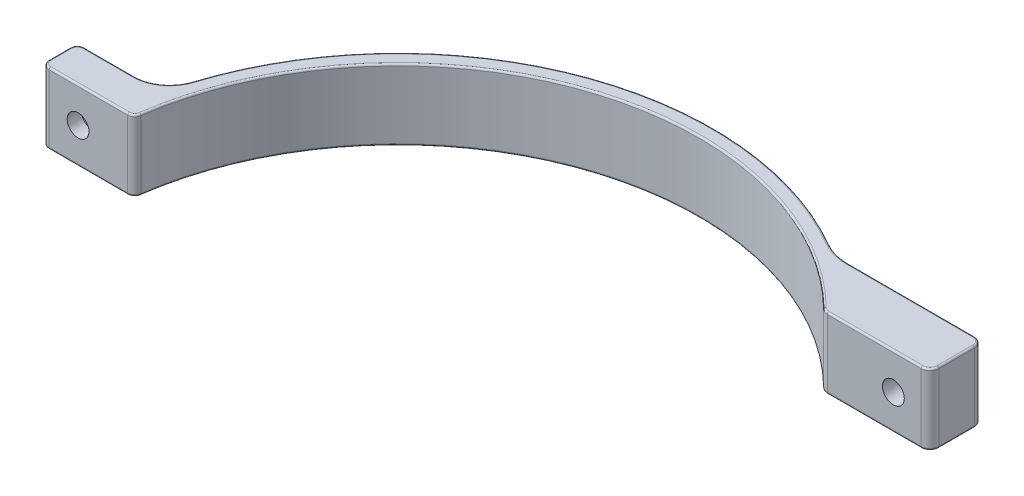
SolidWorks part; units mm, degrees
material "PVC 0.007 Plasticizado"
ref_plane "Plano frontal" through (0, 0, 0) normal (0, 0, 1) x (1, 0, 0)
ref_plane "Plano superior" through (0, 0, 0) normal (0, 1, 0) x (1, 0, 0)
ref_plane "Plano direito" through (0, 0, 0) normal (1, 0, 0) x (0, 0, -1)
sketch "Esboço1" plane through (0, 0, 0) normal (0, 1, 0) x (1, 0, 0)
  line L0 (0, -1000) -> (0, 49000) construction
  line L1 (-1000, 0) -> (49000, 0) construction
  line L3 (61.2372, 60) -> (87.708, 60)
  line L4 (90.208, 62.5) -> (90.208, 72.5)
  line L5 (87.708, 75) -> (52.1153, 75)
  line L7 (-108.4097, 20) -> (-94.3451, 20)
  line L8 (-110.4097, 18) -> (-110.4097, 12)
  line L9 (-108.4097, 10) -> (-86.1684, 10)
  arc A0 (59.4876, 60.7143) -> (-84.1876, 11.7241) centre (0, 0) ccw
  arc A1 (44.5986, 77.0192) -> (-84.8153, 26.9697) centre (0, 0) ccw
  circle A2 centre (0, 0) radius 85 construction
  circle A3 centre (0, 0) radius 89 construction
  arc A4 (44.5986, 77.0192) -> (52.1153, 75) centre (52.1153, 90) ccw
  arc A5 (90.208, 72.5) -> (87.708, 75) centre (87.708, 72.5) ccw
  arc A6 (87.708, 60) -> (90.208, 62.5) centre (87.708, 62.5) ccw
  arc A7 (59.4876, 60.7143) -> (61.2372, 60) centre (61.2372, 62.5) ccw
  arc A11 (-94.3451, 20) -> (-84.8153, 26.9697) centre (-94.3451, 30) ccw
  arc A12 (-84.1876, 11.7241) -> (-86.1684, 10) centre (-86.1684, 12) cw
  arc A13 (-108.4097, 10) -> (-110.4097, 12) centre (-108.4097, 12) cw
  arc A14 (-108.4097, 20) -> (-110.4097, 18) centre (-108.4097, 18) ccw
  point P9 (-177.2056, 15)
  point P25 (90.208, 75)
  point P28 (90.208, 60)
  point P31 (60.208, 60)
  point P34 (-84.4097, 10)
  point P37 (-110.4097, 10)
  point P49 (-110.4097, 10)
  dimension "D1" = 4
  dimension "D4" = 170
  dimension "D5" = 60
  dimension "D8" = 15
  dimension "D9" = 2.5
  dimension "D10" = 2
  dimension "D11" = 10
  dimension "D13" = 2
  dimension "D14" = 2
  dimension "D2" = 26
  dimension "D3" = 15
  dimension "D6" = 30
  dimension "D7" = 10
  dimension "D12" = 10
extrude "Ressalto-extrusão1" add sketch "Esboço1" along normal blind 20
sketch "Esboço3" plane through (0, 0, -60) normal (0, 0, 1) x (1, 0, 0)
  line L1 (61.2372, 20) -> (59.4876, 20) construction
  circle A0 centre (79.8624, 9.7994) radius 3.075
  point P4 (60.3624, 20)
  dimension "D1" = 19.5
extrude "Corte-extrusão1" cut sketch "Esboço3" against normal blind 20
sketch "Esboço4" plane through (0, 0, -75) normal (0, 0, -1) x (-1, 0, 0)
  circle A0 centre (-79.8624, 9.7994) radius 5.25
extrude "Corte-extrusão2" cut sketch "Esboço4" against normal blind 6
sketch "Esboço5" plane through (0, 0, -10) normal (0, 0, 1) x (1, 0, 0)
  line L0 (-108.4097, 20) -> (-86.1684, 20) construction
  line L5 (-108.4097, 20) -> (-108.4097, 0) construction
  circle A0 centre (-100.1797, 10) radius 3.075
  dimension "D1" = 6.15
  dimension "D2" = 10
  dimension "D3" = 8.23
extrude "Corte-extrusão3" cut sketch "Esboço5" against normal through all and the other way through all
sketch "Esboço6" plane through (0, 0, -20) normal (0, 0, -1) x (-1, 0, 0)
  circle A0 centre (100.1797, 10) radius 5.25
extrude "Corte-extrusão4" cut sketch "Esboço6" against normal blind 6
fillet "Filete1" radius 0.5 32 edges at (-32.1027, 0, -83.0085) (-88.4419, 0, -21.9284) (-101.3774, 0, -20) (-109.8239, 0, -19.4142) (-110.4097, 0, -15) (-109.8239, 0, -10.5858) (-97.2891, 0, -10) (-84.8554, 0, -10.4914) (-27.4323, 0, -80.4517) (60.2923, 0, -60.1854) (74.4726, 0, -60) (89.4757, 0, -60.7322) (90.208, 0, -67.5) (89.4757, 0, -74.2678) (69.9116, 0, -75) (48.2237, 0, -75.5136) (69.9116, 20, -75) (89.4757, 20, -74.2678) (90.208, 20, -67.5) (89.4757, 20, -60.7322) (74.4726, 20, -60) (60.2923, 20, -60.1854) (-27.4323, 20, -80.4517) (-84.8554, 20, -10.4914) (-97.2891, 20, -10) (-109.8239, 20, -10.5858) (-110.4097, 20, -15) (-109.8239, 20, -19.4142) (-101.3774, 20, -20) (-88.4419, 20, -21.9284) (-32.1027, 20, -83.0085) (48.2237, 20, -75.5136)
